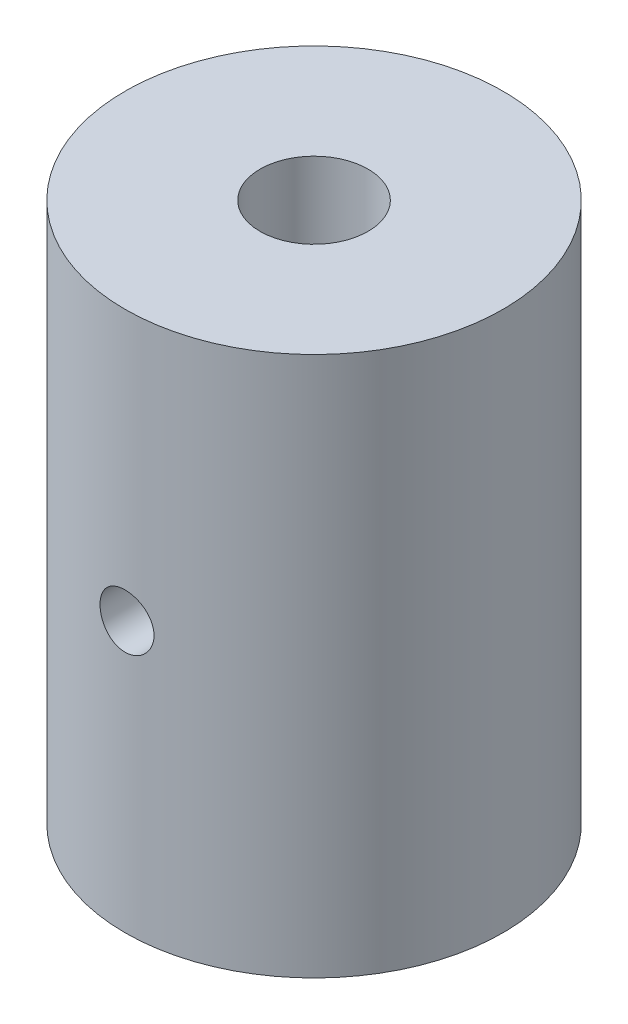
SolidWorks part; units mm, degrees
ref_plane "Front Plane" through (0, 0, 0) normal (0, 0, 1) x (1, 0, 0)
ref_plane "Top Plane" through (0, 0, 0) normal (0, 1, 0) x (1, 0, 0)
ref_plane "Right Plane" through (0, 0, 0) normal (1, 0, 0) x (0, 0, -1)
sketch "Sketch1" plane through (0, 0, 0) normal (0, 1, 0) x (1, 0, 0)
  circle A0 centre (0, 0) radius 1
  circle A1 centre (0, 0) radius 3.5
  point P4 (0, -3.5)
  dimension "D1" = 2
  dimension "D2" = 7
extrude "Boss-Extrude1" add sketch "Sketch1" along normal blind 10
ref_plane "Plane1" through (0, 0, 3.5) normal (0, 0, 1) x (1, 0, 0)
sketch "Sketch2" plane through (0, 0, 3.5) normal (0, 0, 1) x (1, 0, 0)
  circle A0 centre (0, 5) radius 0.5
  point P0 (0, 5)
extrude "Cut-Extrude2" cut sketch "Sketch2" against normal blind 3.5
